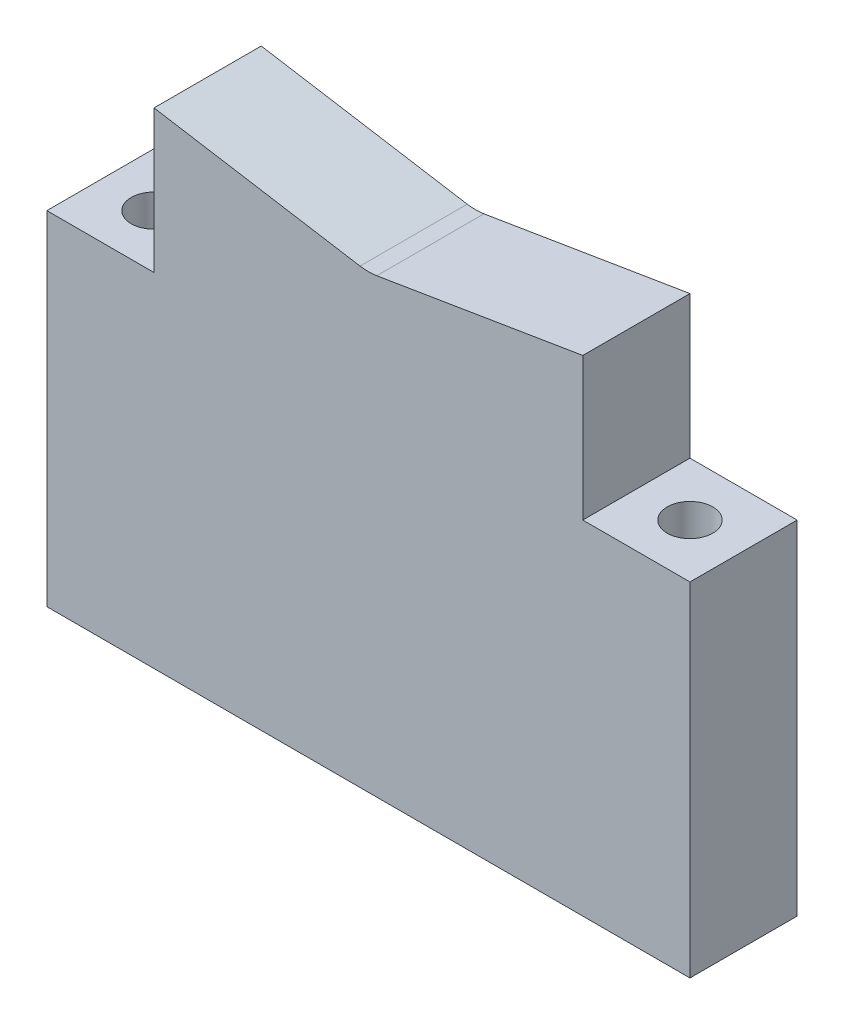
SolidWorks part; units mm, degrees
material "Delrin 2700 NC010, Low Viscosity Acetal Copolymer (SS)"
ref_plane "Front Plane" through (0, 0, 0) normal (0, 0, 1) x (1, 0, 0)
ref_plane "Top Plane" through (0, 0, 0) normal (0, 1, 0) x (1, 0, 0)
ref_plane "Right Plane" through (0, 0, 0) normal (1, 0, 0) x (0, 0, -1)
sketch "Sketch1" plane through (0, 0, 0) normal (0, 0, 1) x (1, 0, 0)
  line L0 (-31.75, 31.75) -> (-31.75, 40.1623)
  line L1 (47.625, -31.75) -> (-47.625, -31.75)
  line L2 (47.625, -31.75) -> (47.625, 31.75)
  line L3 (47.625, 31.75) -> (-47.625, 31.75)
  line L4 (-47.625, -31.75) -> (-47.625, 31.75)
  line L5 (47.625, -31.75) -> (-47.625, 31.75) construction
  line L6 (47.625, 31.75) -> (-47.625, -31.75) construction
  line L7 (-31.75, 40.1623) -> (0, 34.925)
  line L8 (0, 34.925) -> (31.75, 40.1623)
  line L9 (-47.625, 19.05) -> (-31.75, 19.05)
  line L10 (-31.75, 31.75) -> (-31.75, 19.05)
  line L11 (31.75, 40.1623) -> (31.75, 31.75)
  line L13 (47.625, 19.05) -> (31.75, 19.05)
  line L14 (31.75, 31.75) -> (31.75, 19.05)
  circle A0 centre (0, 153.9875) radius 117.475
  point P0 (0, 0)
  dimension "D5" = 234.95
  dimension "D1" = 63.5
  dimension "D2" = 50.8
  dimension "D3" = 15.875
  dimension "D4" = 63.5
  dimension "D6" = 122.2375
  dimension "D7" = 3.175
extrude "Boss-Extrude1" add sketch "Sketch1" along normal blind 15.875 contours L14 L3 L10 L9 L4 L1 L2 L13 | L11 L8 L7 L0 L3
hole_wizard "1/4 Clearance Hole1" positions "Sketch2" profile "Sketch3" hole size "1/4" standard "ANSI Inch" end condition through all
sketch "Sketch2" plane through (0, 19.05, 0) normal (0, 1, 0) x (-1, 0, 0)
  line L0 (-47.625, 0) -> (-31.75, 0) construction
  line L1 (-31.75, 0) -> (-31.75, 15.875) construction
  line L2 (-31.75, 15.875) -> (-47.625, 15.875) construction
  line L3 (-47.625, 15.875) -> (-47.625, 0) construction
  line L4 (31.75, 0) -> (47.625, 0) construction
  line L5 (47.625, 0) -> (47.625, 15.875) construction
  line L6 (47.625, 15.875) -> (31.75, 15.875) construction
  line L7 (31.75, 15.875) -> (31.75, 0) construction
  line L8 (-47.625, 0) -> (-31.75, 0)
  line L9 (-31.75, 0) -> (-31.75, 15.875)
  line L10 (-31.75, 15.875) -> (-47.625, 15.875)
  line L11 (-47.625, 15.875) -> (-47.625, 0)
  line L12 (31.75, 0) -> (47.625, 0)
  line L13 (47.625, 0) -> (47.625, 15.875)
  line L14 (47.625, 15.875) -> (31.75, 15.875)
  line L15 (31.75, 15.875) -> (31.75, 0)
  line L16 (47.625, 7.9375) -> (-47.625, 7.9375) construction
  point P15 (39.6875, 7.9375)
  point P17 (-39.6875, 7.9375)
  dimension "D1" = 7.9375
  dimension "D2" = 7.9375
sketch "Sketch3" plane through (-39.6875, 19.05, 7.9375) normal (1, 0, 0) x (0, 0, 1)
  line L0 (0, 0) -> (0, 50.8)
  line L1 (0, 50.8) -> (3.3782, 50.8)
  line L2 (3.3782, 50.8) -> (3.3782, 0)
  line L5 (3.3782, 0) -> (0, 0)
  line L11 (0, -6.35) -> (0, 107.95) construction
  dimension "Thru Hole Dia." = 6.7564
  dimension "Thru Hole Depth" = 50.8
hole_wizard "1/16 (0.0625) Diameter Hole1" positions "Sketch4" profile "Sketch5" hole size "1/16" standard "ANSI Inch"
sketch "Sketch4" plane through (0, -31.75, 0) normal (0, -1, 0) x (1, 0, 0)
  line L8 (-47.625, 0) -> (47.625, 0)
  line L9 (47.625, 0) -> (47.625, 15.875)
  line L10 (47.625, 15.875) -> (-47.625, 15.875)
  line L11 (-47.625, 15.875) -> (-47.625, 0)
  line L12 (-47.625, 0) -> (47.625, 0)
  line L13 (47.625, 0) -> (47.625, 15.875)
  line L14 (47.625, 15.875) -> (-47.625, 15.875)
  line L15 (-47.625, 15.875) -> (-47.625, 0)
  circle A0 centre (39.6875, 7.9375) radius 3.3782 construction
  circle A1 centre (-39.6875, 7.9375) radius 3.3782 construction
  circle A2 centre (39.6875, 7.9375) radius 3.3782
  circle A3 centre (-39.6875, 7.9375) radius 3.3782
  point P15 (39.6875, 7.9375)
  point P17 (-39.6875, 7.9375)
  dimension "D1" = 0
sketch "Sketch5" plane through (39.6875, -31.75, 7.9375) normal (1, 0, 0) x (0, 0, -1)
  line L0 (0, 0) -> (0, 33.3756)
  line L1 (0, 33.3756) -> (5.715, 33.3756)
  line L2 (5.715, 33.3756) -> (5.715, 0)
  line L5 (5.715, 0) -> (0, 0)
  line L10 (0, 33.3756) -> (-5.715, 33.3756) construction
  line L11 (0, -6.35) -> (0, 107.95) construction
  dimension "Hole Dia." = 11.43
  dimension "Hole Depth" = 33.3756
  dimension "Drill Angle" = 180
fillet "Fillet1" radius 7.62 1 edges at (0, 34.925, 7.9375)
